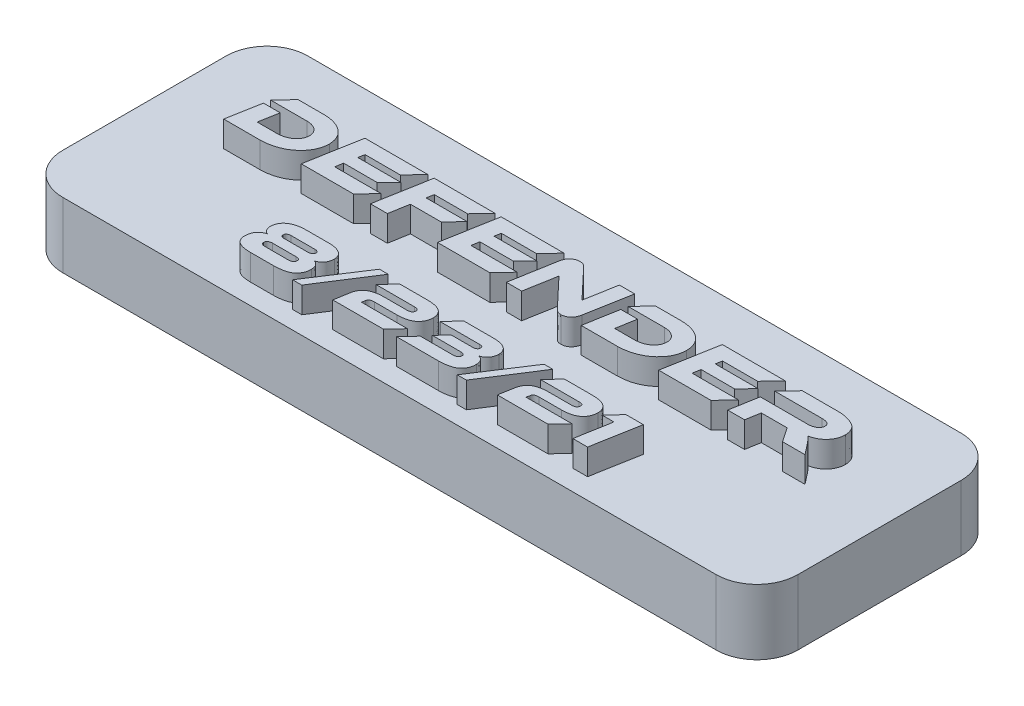
SolidWorks part; units mm, degrees
ref_plane "Front Plane" through (0, 0, 0) normal (0, 0, 1) x (1, 0, 0)
ref_plane "Top Plane" through (0, 0, 0) normal (0, 1, 0) x (1, 0, 0)
ref_plane "Right Plane" through (0, 0, 0) normal (1, 0, 0) x (0, 0, -1)
sketch "Sketch1" plane through (0, 0, 0) normal (0, 1, 0) x (1, 0, 0)
  line L1 (-28.575, 9.525) -> (28.575, 9.525)
  line L2 (-28.575, 9.525) -> (-28.575, -9.525)
  line L3 (-28.575, -9.525) -> (28.575, -9.525)
  line L4 (28.575, 9.525) -> (28.575, -9.525)
  line L5 (-28.575, 9.525) -> (28.575, -9.525) construction
  line L6 (-28.575, -9.525) -> (28.575, 9.525) construction
  point P0 (0, 0)
  dimension "D1" = 57.15
  dimension "D2" = 19.05
extrude "Boss-Extrude1" add sketch "Sketch1" along normal up to surface (5.08 mm away)
fillet "Fillet1" radius 3.175 4 edges at (-28.575, 2.54, 9.525) (-28.575, 2.54, -9.525) (28.575, 2.54, 9.525) (28.575, 2.54, -9.525)
sketch "Sketch3" plane through (0, 5.08, 0) normal (0, 1, 0) x (1, 0, 0)
  line L0 (28.575, -7.9375) -> (-28.575, -7.9375) construction
  line L1 (28.575, -6.35) -> (28.575, 6.35) construction
  line L2 (-28.575, 6.35) -> (-28.575, -6.35) construction
  line L3 (28.575, 0) -> (-28.575, 0) construction
  line L5 (-25.4, -9.525) -> (25.4, -9.525) construction
  line L6 (25.4, 9.525) -> (-25.4, 9.525) construction
  text T0 "DEFENDER" font "Ethnocentric Rg" height in points 16
  text T1 "8/23/21\r\n" font "Ethnocentric Rg" height in points 14
  point P8 (-28.575, 0)
  dimension "D1" = 1.5875
extrude "Boss-Extrude2" add sketch "Sketch3" along normal blind 2
sketch "Sketch4" plane through (0, 0, 0) normal (0, -1, 0) x (1, 0, 0)
  line L0 (25.4, 0) -> (-25.4, 0) construction
  circle A0 centre (-25.4, 0) radius 0.9
  circle A1 centre (25.4, 0) radius 0.9
  point P3 (0, 0)
  dimension "D2" = 1.8
  dimension "D1" = 50.8
extrude "Cut-Extrude1" cut sketch "Sketch4" against normal blind 4
